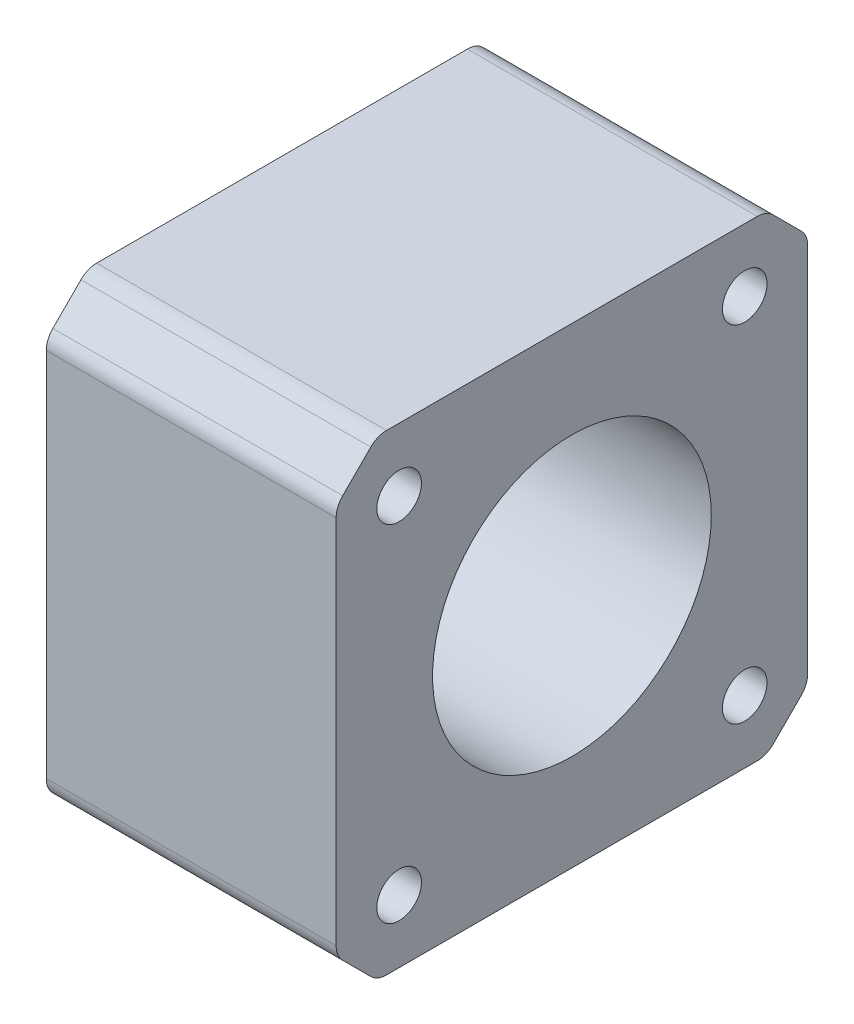
SolidWorks part; units mm, degrees
ref_plane "Front Plane" through (0, 0, 0) normal (0, 0, 1) x (1, 0, 0)
ref_plane "Top Plane" through (0, 0, 0) normal (0, 1, 0) x (1, 0, 0)
ref_plane "Right Plane" through (0, 0, 0) normal (1, 0, 0) x (0, 0, -1)
sketch "Sketch1" plane through (0, 0, 0) normal (1, 0, 0) x (0, 0, -1)
  line L0 (-21.15, 17.458) -> (-17.458, 21.15)
  line L1 (-17.458, 21.15) -> (17.458, 21.15)
  line L2 (-21.15, 17.458) -> (-21.15, -17.458)
  line L3 (-17.458, -21.15) -> (17.458, -21.15)
  line L4 (21.15, 17.458) -> (21.15, -17.458)
  line L7 (17.458, 21.15) -> (21.15, 17.458)
  line L8 (17.458, -21.15) -> (21.15, -17.458)
  line L9 (-17.458, -21.15) -> (-21.15, -17.458)
  dimension "D1" = 42.3
  dimension "D2" = 42.3
  dimension "D3" = 135
  dimension "D4" = 135
  dimension "D5" = 54.6
  dimension "D6" = 54.6
  dimension "D7" = 21.15
  dimension "D8" = 21.15
  dimension "D9" = 27.3
  dimension "D10" = 27.3
extrude "Boss-Extrude1" add sketch "Sketch1" along normal blind 26
fillet "Fillet1" radius 2 8 edges at (13, -17.458, -21.15) (13, -21.15, -17.458) (13, -21.15, 17.458) (13, -17.458, 21.15) (13, 17.458, 21.15) (13, 21.15, 17.458) (13, 21.15, -17.458) (13, 17.458, -21.15)
sketch "Sketch2" plane through (26, 0, 0) normal (1, 0, 0) x (0, 0, -1)
  circle A0 centre (0, 0) radius 12.5
  dimension "D1" = 25
extrude "Cut-Extrude1" cut sketch "Sketch2" against normal through all
sketch "Sketch3" plane through (26, 0, 0) normal (1, 0, 0) x (0, 0, -1)
  circle A0 centre (-15.5, 15.5) radius 2
  dimension "D1" = 4
  dimension "D2" = 15.5
  dimension "D3" = 15.5
extrude "Cut-Extrude2" cut sketch "Sketch3" against normal through all
pattern_linear "LPattern1" count 2 spacing 31 along (0, 0, -1) of "Cut-Extrude2"
mirror "Mirror1" about plane through (0, 0, 0) normal (0, 1, 0) of "LPattern1", "Cut-Extrude2"
